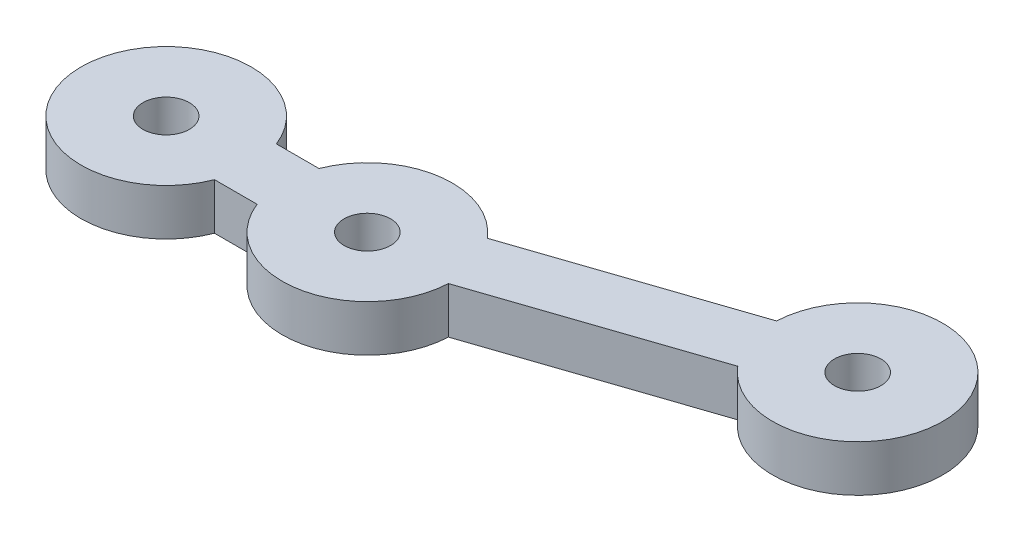
SolidWorks part; units mm, degrees
ref_plane "Front Plane" through (0, 0, 0) normal (0, 0, 1) x (1, 0, 0)
ref_plane "Top Plane" through (0, 0, 0) normal (0, 1, 0) x (1, 0, 0)
ref_plane "Right Plane" through (0, 0, 0) normal (1, 0, 0) x (0, 0, -1)
sketch "Sketch1" plane through (0, 0, 0) normal (0, 1, 0) x (1, 0, 0)
  line L0 (0, 0) -> (13, 0)
  line L1 (13, 0) -> (36.6854, 8)
  line L2 (0, -2) -> (13.3286, -2)
  line L3 (13.3286, -2) -> (37.3254, 6.1052)
  line L4 (0, 2) -> (12.6714, 2)
  line L5 (12.6714, 2) -> (36.0454, 9.8948)
  circle A0 centre (0, 0) radius 1.5
  circle A1 centre (13, 0) radius 1.5
  circle A2 centre (36.6854, 8) radius 1.5
  circle A3 centre (0, 0) radius 5.5
  circle A4 centre (13, 0) radius 5.5
  circle A5 centre (36.6854, 8) radius 5.5
  dimension "D2" = 3
  dimension "D8" = 11
  dimension "D1" = 13
  dimension "D3" = 25
  dimension "D4" = 8
  dimension "D5" = 4
  dimension "D6" = 2
  dimension "D7" = 2
extrude "Boss-Extrude1" add sketch "Sketch1" along normal blind 3
